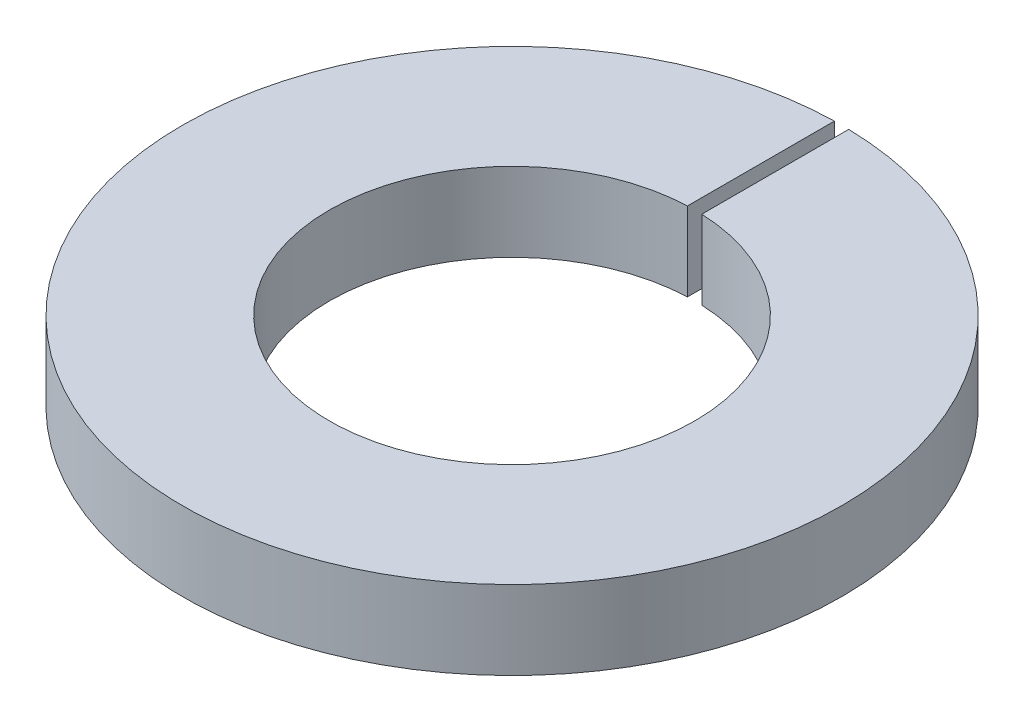
SolidWorks part; units mm, degrees
material "1.4057 (X17CrNi16-2)"
ref_plane "Plano frontal" through (0, 0, 0) normal (0, 0, 1) x (1, 0, 0)
ref_plane "Plano superior" through (0, 0, 0) normal (0, 1, 0) x (1, 0, 0)
ref_plane "Plano direito" through (0, 0, 0) normal (1, 0, 0) x (0, 0, -1)
sketch "Esboço1" plane through (0, 0, 0) normal (0, 1, 0) x (1, 0, 0)
  line L0 (-0.1, 4.5989) -> (-0.1, 2.548)
  line L1 (0.1, 4.5989) -> (0.1, 2.548)
  line L2 (0, 0) -> (0, 4.1585) construction
  line L3 (0.1, 3.5735) -> (0, 3.5735) construction
  line L4 (0, 3.5735) -> (-0.1, 3.5735) construction
  arc A2 (-0.1, 2.548) -> (0.1, 2.548) centre (0, 0) ccw
  arc A3 (-0.1, 4.5989) -> (0.1, 4.5989) centre (0, 0) ccw
  dimension "D1" = 2.55
  dimension "D2" = 4.6
  dimension "D3" = 0.2
extrude "Ressalto-extrusão1" add sketch "Esboço1" along normal blind 1.1
